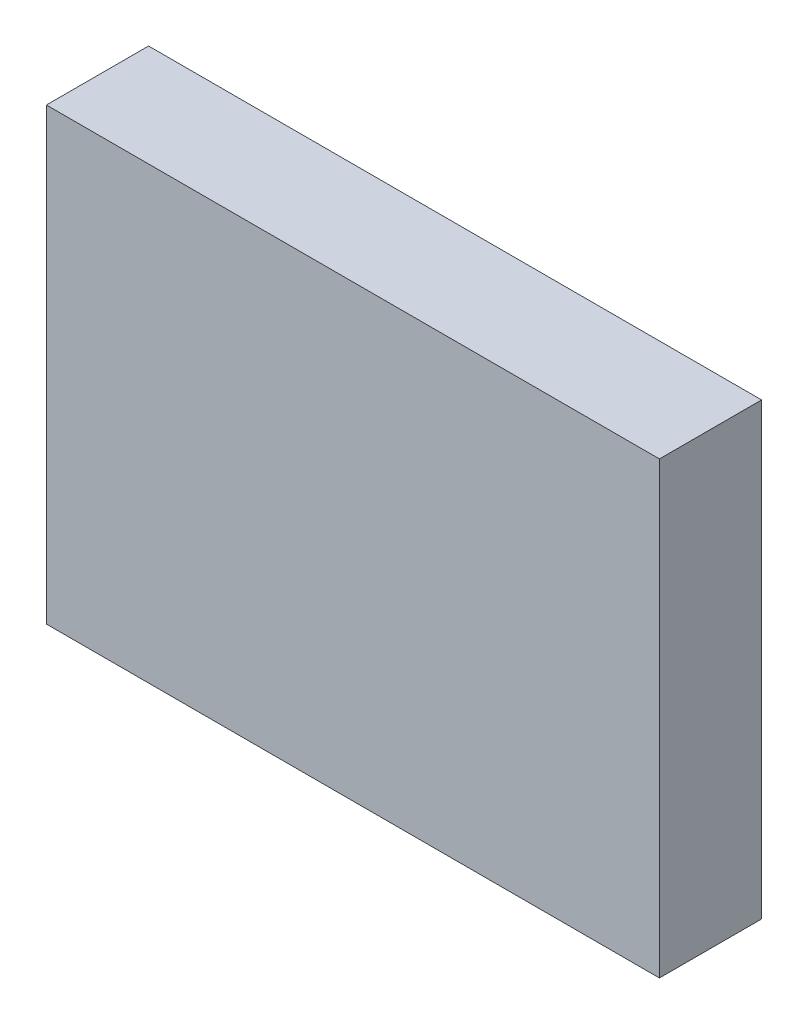
SolidWorks part; units mm, degrees
ref_plane "Plan de face" through (0, 0, 0) normal (0, 0, 1) x (1, 0, 0)
ref_plane "Plan de dessus" through (0, 0, 0) normal (0, 1, 0) x (1, 0, 0)
ref_plane "Plan de droite" through (0, 0, 0) normal (1, 0, 0) x (0, 0, -1)
sketch "Esquisse1" plane through (0, 0, 0) normal (0, 0, 1) x (1, 0, 0)
  line L1 (-7.5, 5.5) -> (7.5, 5.5)
  line L2 (-7.5, 5.5) -> (-7.5, -5.5)
  line L3 (-7.5, -5.5) -> (7.5, -5.5)
  line L4 (7.5, 5.5) -> (7.5, -5.5)
  line L5 (-7.5, 5.5) -> (7.5, -5.5) construction
  line L6 (-7.5, -5.5) -> (7.5, 5.5) construction
  point P0 (0, 0)
  dimension "D1" = 15
  dimension "D2" = 11
extrude "Boss.-Extru.1" add sketch "Esquisse1" along normal blind 2.5
